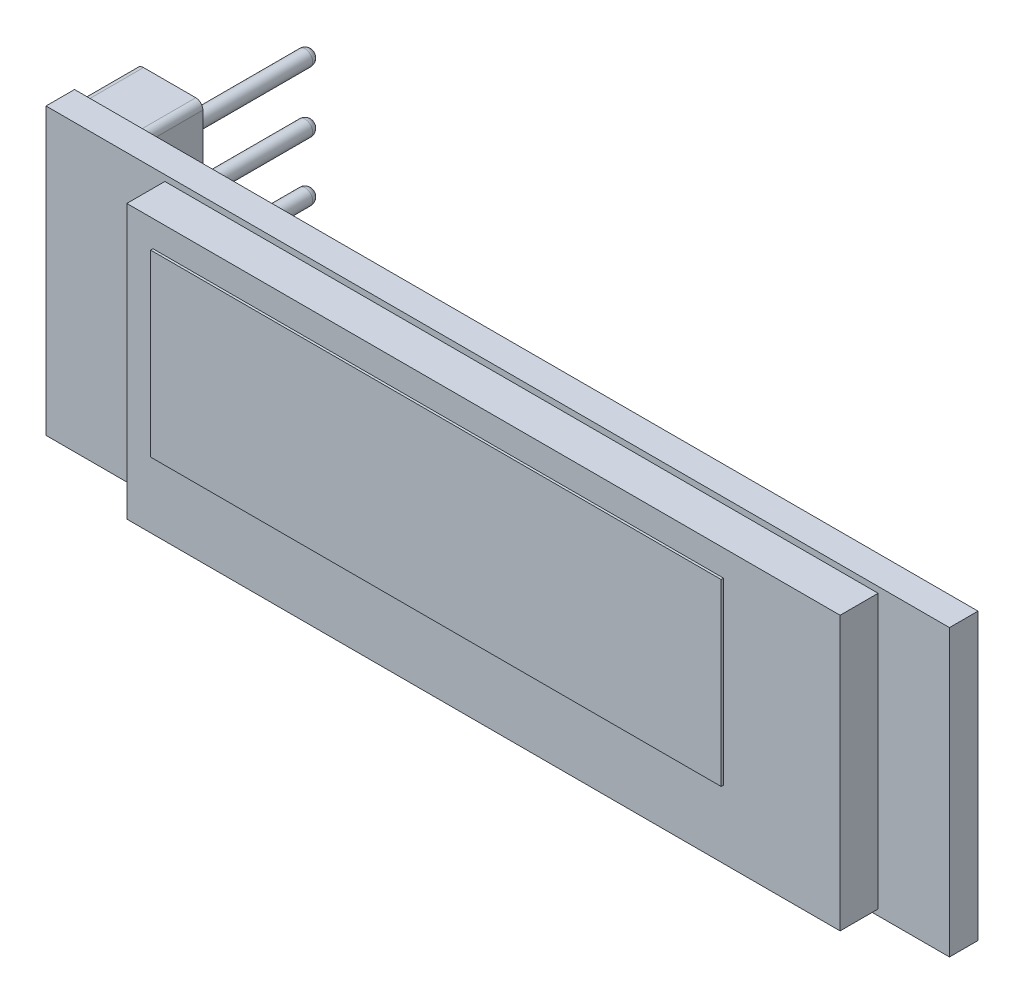
SolidWorks part; units mm, degrees
ref_plane "Front Plane" through (0, 0, 0) normal (0, 0, 1) x (1, 0, 0)
ref_plane "Top Plane" through (0, 0, 0) normal (0, 1, 0) x (1, 0, 0)
ref_plane "Right Plane" through (0, 0, 0) normal (1, 0, 0) x (0, 0, -1)
sketch "Sketch1" plane through (0, 0, 0) normal (0, 0, 1) x (1, 0, 0)
  line L1 (19, -6) -> (-19, -6)
  line L2 (19, -6) -> (19, 6)
  line L3 (19, 6) -> (-19, 6)
  line L4 (-19, -6) -> (-19, 6)
  line L5 (19, -6) -> (-19, 6) construction
  line L6 (19, 6) -> (-19, -6) construction
  point P0 (0, 0)
  dimension "D1" = 38
  dimension "D2" = 12
extrude "Boss-Extrude1" add sketch "Sketch1" along normal blind 1.2
sketch "Sketch2" plane through (0, 0, 1.2) normal (0, 0, 1) x (1, 0, 0)
  line L0 (-19, 6) -> (-19, -6) construction
  line L1 (-14, -5.75) -> (16, -5.75)
  line L2 (-14, -5.75) -> (-14, 5.75)
  line L3 (-14, 5.75) -> (16, 5.75)
  line L4 (16, -5.75) -> (16, 5.75)
  line L5 (-14, -5.75) -> (16, 5.75) construction
  line L6 (-14, 5.75) -> (16, -5.75) construction
  line L7 (-19, 0) -> (19, 0) construction
  line L8 (19, -6) -> (19, 6) construction
  point P0 (1, 0)
  point P7 (0, 0)
  dimension "D1" = 5
  dimension "D2" = 11.5
  dimension "D3" = 30
extrude "Boss-Extrude2" add sketch "Sketch2" along normal blind 1.6
sketch "Sketch4" plane through (0, 0, 2.8) normal (0, 0, 1) x (1, 0, 0)
  line L0 (-14, 0) -> (16, 0) construction
  line L1 (-14, 5.75) -> (-14, -5.75) construction
  line L2 (16, -5.75) -> (16, 5.75) construction
  line L3 (-19, 6) -> (-19, -6) construction
  line L4 (-12.9, 4.65) -> (11.1, 4.65)
  line L5 (-12.9, 4.65) -> (-12.9, -2.89)
  line L6 (-12.9, -2.89) -> (11.1, -2.89)
  line L7 (11.1, 4.65) -> (11.1, -2.89)
  line L8 (-12.9, 4.65) -> (11.1, -2.89) construction
  line L9 (-12.9, -2.89) -> (11.1, 4.65) construction
  line L10 (16, 5.75) -> (-14, 5.75) construction
  point P6 (-0.9, 0.88)
  dimension "D1" = 7.54
  dimension "D2" = 24
  dimension "D3" = 6.1
  dimension "D4" = 1.1
sketch "Sketch5" plane through (0, 0, 0) normal (0, 0, -1) x (-1, 0, 0)
  line L0 (17.5, 6) -> (17.5, -6) construction
  line L1 (-19, 6) -> (19, 6) construction
  line L2 (19, -6) -> (-19, -6) construction
  line L3 (19, 6) -> (19, -6) construction
  circle A0 centre (17.5, 3.81) radius 0.32
  circle A1 centre (17.5, 1.25) radius 0.32
  circle A2 centre (17.5, -1.25) radius 0.32
  circle A3 centre (17.5, -3.81) radius 0.32
  point P16 (0, 0)
  dimension "D2" = 0.64
  dimension "D1" = 1.5
  dimension "D3" = 7.62
  dimension "D4" = 2.56
  dimension "D5" = 2.56
  dimension "D6" = 2.19
sketch "Sketch6" plane through (0, 0, 0) normal (0, 0, -1) x (-1, 0, 0)
  line L0 (17.5, 6) -> (17.5, -6) construction
  line L1 (18.9, -5.75) -> (16.1, -5.75)
  line L2 (18.9, -5.75) -> (18.9, 5.75)
  line L3 (18.9, 5.75) -> (16.1, 5.75)
  line L4 (16.1, -5.75) -> (16.1, 5.75)
  line L5 (18.9, -5.75) -> (16.1, 5.75) construction
  line L6 (18.9, 5.75) -> (16.1, -5.75) construction
  point P0 (17.5, 0)
  dimension "D1" = 2.8
  dimension "D2" = 11.5
extrude "Boss-Extrude4" add sketch "Sketch6" along normal blind 2.5
extrude "Boss-Extrude5" add sketch "Sketch5" along normal blind 8.5
fillet "Fillet1" radius 0.3 4 edges at (-17.82, -3.81, -8.5) (-17.82, -1.25, -8.5) (-17.82, 1.25, -8.5) (-17.82, 3.81, -8.5)
fillet "Fillet2" radius 0.3 4 edges at (-16.1, 5.75, -1.25) (-18.9, 5.75, -1.25) (-16.1, -5.75, -1.25) (-18.9, -5.75, -1.25)
extrude "Boss-Extrude6" add sketch "Sketch4" along normal blind 0.1
